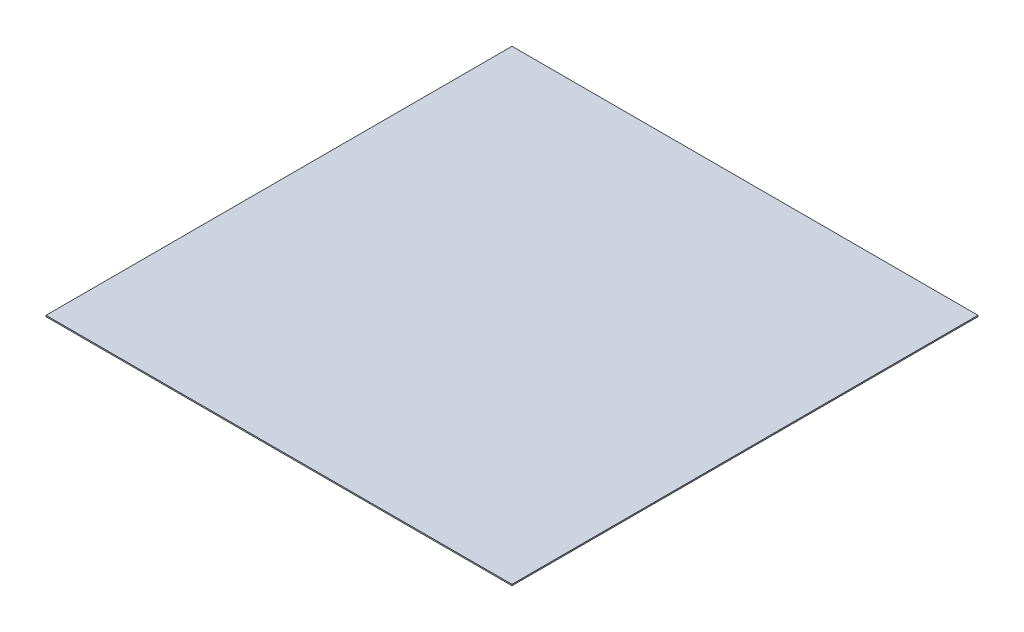
SolidWorks part; units mm, degrees
ref_plane "Front Plane" through (0, 0, 0) normal (0, 0, 1) x (1, 0, 0)
ref_plane "Top Plane" through (0, 0, 0) normal (0, 1, 0) x (1, 0, 0)
ref_plane "Right Plane" through (0, 0, 0) normal (1, 0, 0) x (0, 0, -1)
sketch "Sketch1" plane through (0, 0, 0) normal (0, 1, 0) x (1, 0, 0)
  line L1 (75, -75) -> (-75, -75)
  line L2 (75, -75) -> (75, 75)
  line L3 (75, 75) -> (-75, 75)
  line L4 (-75, -75) -> (-75, 75)
  line L5 (75, -75) -> (-75, 75) construction
  line L6 (75, 75) -> (-75, -75) construction
  point P0 (0, 0)
  dimension "D1" = 150
  dimension "D2" = 150
extrude "Boss-Extrude1" add sketch "Sketch1" along normal blind 0.4
